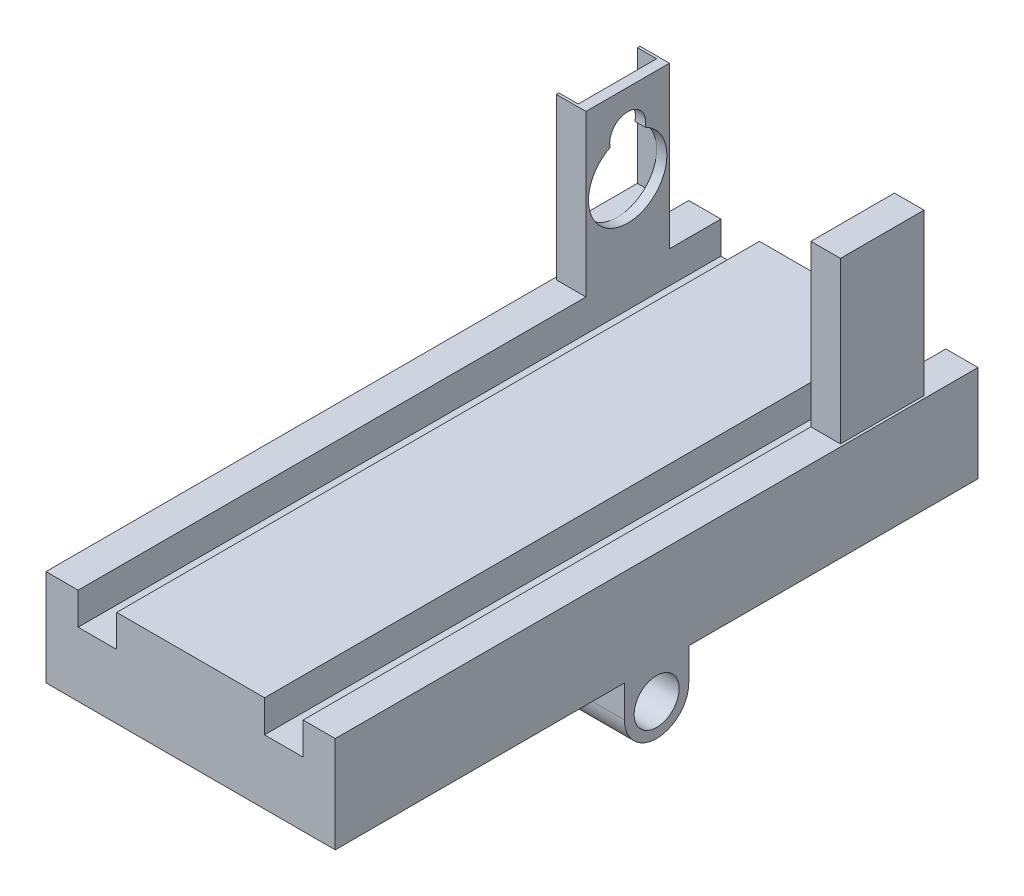
SolidWorks part; units mm, degrees
ref_plane "Front Plane" through (0, 0, 0) normal (0, 0, 1) x (1, 0, 0)
ref_plane "Top Plane" through (0, 0, 0) normal (0, 1, 0) x (1, 0, 0)
ref_plane "Right Plane" through (0, 0, 0) normal (1, 0, 0) x (0, 0, -1)
sketch "Sketch1" plane through (0, 0, 0) normal (0, 0, 1) x (1, 0, 0)
  line L0 (-11.5, 5) -> (11.5, 5)
  line L1 (-11.5, 5) -> (-11.5, 0)
  line L2 (11.5, 5) -> (11.5, 0)
  line L3 (11.5, 0) -> (17.5, 0)
  line L4 (-11.5, 0) -> (-17.5, 0)
  line L5 (-17.5, 0) -> (-17.5, 5)
  line L6 (-17.5, 5) -> (-22.5, 5)
  line L7 (-22.5, 5) -> (-22.5, -10)
  line L8 (-22.5, -10) -> (22.5, -10)
  line L9 (22.5, -10) -> (22.5, 5)
  line L10 (22.5, 5) -> (17.5, 5)
  line L11 (17.5, 5) -> (17.5, 0)
  point P2 (0, 5)
  dimension "D1" = 23
  dimension "D2" = 5
  dimension "D3" = 6
  dimension "D4" = 15
  dimension "D5" = 45
extrude "Boss-Extrude1" add sketch "Sketch1" along normal blind 100
sketch "Sketch2" plane through (-22.5, 0, 0) normal (-1, 0, 0) x (0, 0, 1)
  line L0 (100, -10) -> (0, -10) construction
  line L1 (45, -15) -> (45, -10)
  line L2 (55, -15) -> (55, -10)
  line L3 (45, -10) -> (55, -10)
  line L4 (45, -15) -> (55, -15)
  point P0 (50, -15)
  point P4 (50, -10)
  dimension "D1" = 5
  dimension "D2" = 10
extrude "Boss-Extrude3" add sketch "Sketch2" against normal blind 45
sketch "Sketch3" plane through (-22.5, 0, 0) normal (-1, 0, 0) x (0, 0, 1)
  line L0 (45, -15) -> (55, -15) construction
  circle A0 centre (50, -15) radius 5
  circle A1 centre (50, -15) radius 2.85
  dimension "D1" = 5.7
extrude "Boss-Extrude4" add sketch "Sketch3" against normal blind 45 contours A0
sketch "Sketch4" plane through (-22.5, 0, 0) normal (-1, 0, 0) x (0, 0, 1)
  circle A0 centre (50, -15) radius 3.5
  arc A1 (45, -15) -> (55, -15) centre (50, -15) ccw construction
  point P7 (50, -20)
  dimension "D1" = 7
extrude "Cut-Extrude1" cut sketch "Sketch4" against normal blind 45
sketch "Sketch5" plane through (0, 5, 0) normal (0, 1, 0) x (1, 0, 0)
  line L1 (-22.1, -8) -> (-17.5, -8)
  line L2 (-22.1, -8) -> (-22.1, -21)
  line L3 (-22.1, -21) -> (-17.5, -21)
  line L4 (-17.5, -8) -> (-17.5, -21)
  line L5 (-17.5, -100) -> (-17.5, 0) construction
  line L6 (-17.5, 0) -> (-22.5, 0) construction
  line L7 (17.5, -100) -> (17.5, 0) construction
  line L8 (17.5, -8) -> (22.1, -8)
  line L9 (17.5, -8) -> (17.5, -21)
  line L10 (17.5, -21) -> (22.1, -21)
  line L11 (22.1, -8) -> (22.1, -21)
  dimension "D1" = 8
  dimension "D2" = 13
  dimension "D3" = 4.6
  dimension "D4" = 13
  dimension "D5" = 4.6
extrude "Boss-Extrude5" add sketch "Sketch5" along normal blind 25
sketch "Sketch6" plane through (-17.5, 0, 0) normal (1, 0, 0) x (0, 0, -1)
  line L0 (-21, 30) -> (-8, 30) construction
  line L1 (-100, 5) -> (0, 5) construction
  line L2 (-17.3, 23.9) -> (-17.3, 23.2194)
  line L3 (-11.7, 23.9) -> (-11.7, 23.2194)
  circle A0 centre (-14.5, 17.8) radius 6.1
  circle A1 centre (-14.5, 23.9) radius 2.8
  point P4 (-14.5, 30)
  dimension "D2" = 12.2
  dimension "D3" = 5.6
  dimension "D1" = 12.8
extrude "Cut-Extrude2" cut sketch "Sketch6" against normal blind 25 contours A1 | A0
sketch "Sketch7" plane through (-22.1, 0, 0) normal (-1, 0, 0) x (0, 0, 1)
  line L0 (8, 30) -> (21, 30) construction
  line L1 (8.4, 34.2) -> (20.6, 34.2)
  line L2 (8.4, 34.2) -> (8.4, 11.7)
  line L3 (8.4, 11.7) -> (20.6, 11.7)
  line L4 (20.6, 34.2) -> (20.6, 11.7)
  arc A0 (11.7747, 23.2574) -> (17.2253, 23.2574) centre (14.5, 17.8) ccw construction
  point P6 (14.5, 30)
  point P7 (14.5, 34.2)
  dimension "D1" = 12.2
  dimension "D2" = 22.5
extrude "Cut-Extrude3" cut sketch "Sketch7" against normal blind 3
